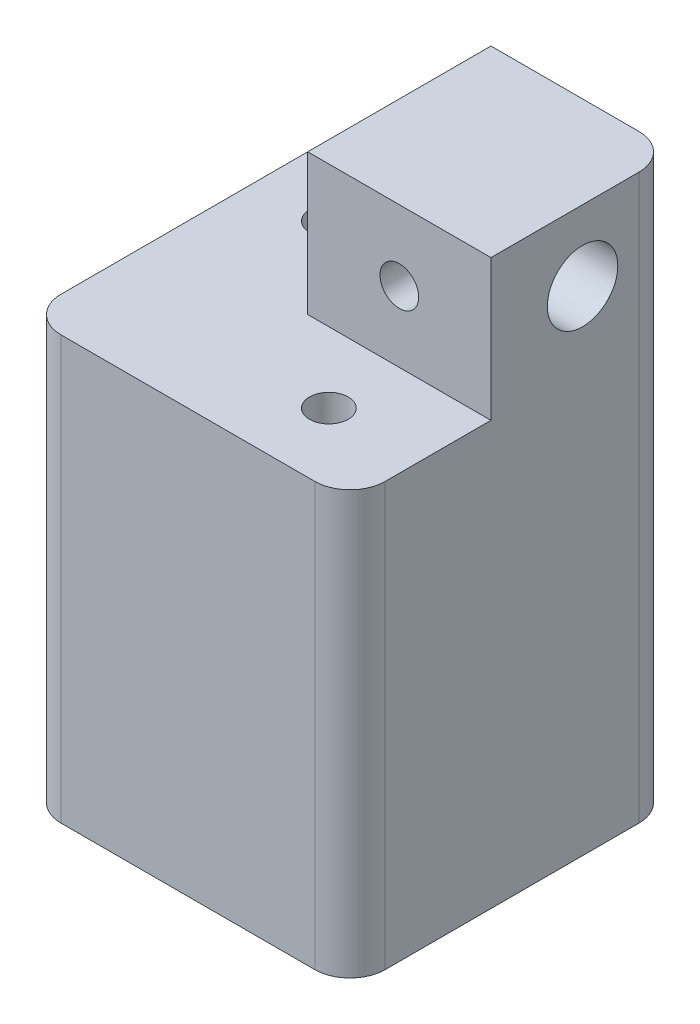
SolidWorks part; units mm, degrees
material "ABS"
ref_plane "Front Plane" through (0, 0, 0) normal (0, 0, 1) x (1, 0, 0)
ref_plane "Top Plane" through (0, 0, 0) normal (0, 1, 0) x (1, 0, 0)
ref_plane "Right Plane" through (0, 0, 0) normal (1, 0, 0) x (0, 0, -1)
sketch "Sketch1" plane through (0, 0, 0) normal (0, 1, 0) x (1, 0, 0)
  line L1 (0, 0) -> (46, 0)
  line L2 (0, 0) -> (0, 46)
  line L3 (0, 46) -> (46, 46)
  line L4 (46, 0) -> (46, 46)
  dimension "D1" = 46
  dimension "D2" = 46
extrude "Boss-Extrude1" add sketch "Sketch1" along normal blind 80
sketch "Sketch2" plane through (0, 80, 0) normal (0, 1, 0) x (1, 0, 0)
  line L0 (0, 0) -> (46, 0) construction
  line L1 (0, 46) -> (20, 46)
  line L2 (0, 46) -> (0, 0)
  line L3 (0, 0) -> (20, 0)
  line L4 (20, 46) -> (20, 20)
  line L5 (46, 0) -> (46, 46) construction
  line L6 (20, 0) -> (46, 0)
  line L8 (20, 20) -> (46, 20)
  line L9 (46, 0) -> (46, 20)
  dimension "D1" = 20
  dimension "D2" = 20
extrude "Cut-Extrude1" cut sketch "Sketch2" against normal blind 20
sketch "Sketch3" plane through (46, 0, 0) normal (1, 0, 0) x (0, 0, -1)
  line L0 (20, 70) -> (46, 70) construction
  line L1 (20, 60) -> (20, 80) construction
  line L2 (46, 80) -> (46, 0) construction
  line L3 (33, 80) -> (33, 0) construction
  line L4 (20, 80) -> (46, 80) construction
  line L5 (0, 0) -> (46, 0) construction
  circle A0 centre (33, 70) radius 5
  dimension "D1" = 10
extrude "Cut-Extrude2" cut sketch "Sketch3" against normal blind 21
sketch "Sketch4" plane through (0, 0, -46) normal (0, 0, -1) x (-1, 0, 0)
  line L0 (-33, 80) -> (-33, 0) construction
  line L1 (-46, 80) -> (-20, 80) construction
  line L2 (-46, 0) -> (0, 0) construction
  line L3 (-20, 70) -> (-46, 70) construction
  line L4 (-20, 60) -> (-20, 80) construction
  line L5 (-46, 80) -> (-46, 0) construction
  circle A0 centre (-33, 70) radius 5
  dimension "D1" = 10
extrude "Cut-Extrude3" cut sketch "Sketch4" against normal blind 21
sketch "Sketch5" plane through (0, 0, -46) normal (0, 0, -1) x (-1, 0, 0)
  line L0 (-33, 80) -> (-33, 0) construction
  line L1 (-46, 80) -> (-20, 80) construction
  line L2 (-46, 0) -> (0, 0) construction
  line L3 (-20, 70) -> (-46, 70) construction
  line L4 (-20, 60) -> (-20, 80) construction
  line L5 (-46, 80) -> (-46, 0) construction
  circle A0 centre (-33, 70) radius 2.75
  dimension "D1" = 5.5
extrude "Cut-Extrude4" cut sketch "Sketch5" against normal through all
sketch "Sketch6" plane through (46, 0, 0) normal (1, 0, 0) x (0, 0, -1)
  line L0 (33, 80) -> (33, 0) construction
  line L1 (20, 80) -> (46, 80) construction
  line L2 (0, 0) -> (46, 0) construction
  line L3 (20, 70) -> (46, 70) construction
  line L4 (20, 60) -> (20, 80) construction
  line L5 (46, 80) -> (46, 0) construction
  circle A0 centre (33, 70) radius 2.75
  dimension "D1" = 5.5
extrude "Cut-Extrude5" cut sketch "Sketch6" against normal through all
fillet "Fillet1" radius 5 4 edges at (0, 30, -46) (0, 30, 0) (46, 30, 0) (46, 40, -46)
sketch "Sketch9" plane through (0, 0, 0) normal (0, -1, 0) x (1, 0, 0)
  line L0 (20, -33) -> (0, -33) construction
  line L1 (20, -20) -> (20, -46) construction
  line L2 (0, -41) -> (0, -5) construction
  circle A0 centre (10, -33) radius 2.75
  dimension "D1" = 5.5
extrude "Cut-Extrude8" cut sketch "Sketch9" against normal through all
sketch "Sketch10" plane through (0, 60, 0) normal (0, 1, 0) x (1, 0, 0)
  line L0 (33, 20) -> (33, 0) construction
  line L1 (46, 20) -> (20, 20) construction
  line L2 (5, 0) -> (41, 0) construction
  circle A0 centre (33, 10) radius 2.75
  dimension "D1" = 5.5
extrude "Cut-Extrude9" cut sketch "Sketch10" against normal through all
sketch "Sketch11" plane through (0, 0, 0) normal (0, -1, 0) x (1, 0, 0)
  circle A0 centre (33, -10) radius 5
  circle A1 centre (10, -33) radius 5
  dimension "D1" = 10
  dimension "D2" = 10
extrude "Cut-Extrude10" cut sketch "Sketch11" against normal blind 55
